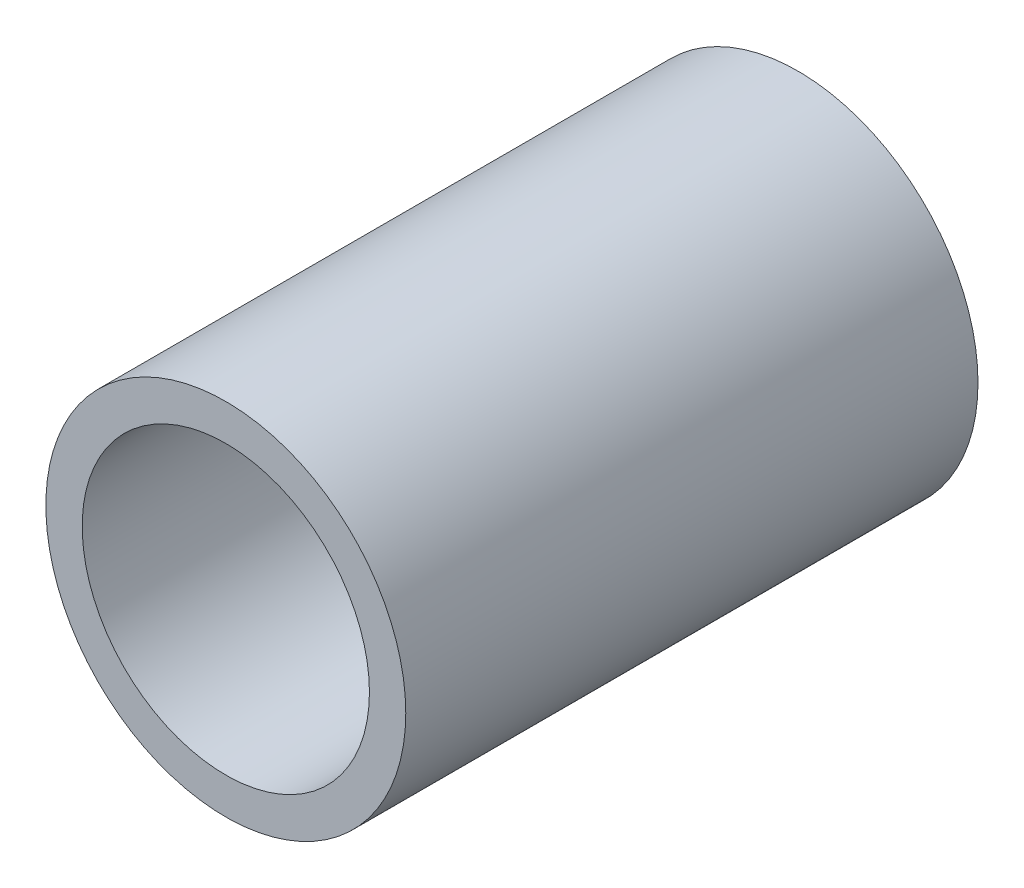
SolidWorks part; units mm, degrees
ref_plane "Front Plane" through (0, 0, 0) normal (0, 0, 1) x (1, 0, 0)
ref_plane "Top Plane" through (0, 0, 0) normal (0, 1, 0) x (1, 0, 0)
ref_plane "Right Plane" through (0, 0, 0) normal (1, 0, 0) x (0, 0, -1)
sketch "Sketch1" plane through (0, 0, 0) normal (0, 0, 1) x (1, 0, 0)
  circle A0 centre (0, 0) radius 3.9942
  circle A1 centre (0, 0) radius 3.1877
  dimension "D1" = 7.9883
  dimension "ID" = 6.3754
extrude "Extrude1" add sketch "Sketch1" along normal mid plane 12.7
sketch "Sketch2" plane through (0, 0, 0) normal (1, 0, 0) x (0, 0, -1)
  line L0 (-6.35, -3.1877) -> (6.35, -3.1877) construction
  line L3 (6.35, 3.1877) -> (-6.35, 3.1877) construction
  line L5 (-6.35, -3.1877) -> (6.35, -3.1877)
  line L6 (6.35, 3.1877) -> (-6.35, 3.1877)
sketch "Sketch4" plane through (0, 0, 6.35) normal (0, 0, 1) x (1, 0, 0)
  line L0 (0, 0) -> (-2.254, 2.254)
  line L1 (0, -10.4775) -> (0, 10.4775) construction
  circle A0 centre (0, 0) radius 3.1877 construction
  dimension "D1" = 45
